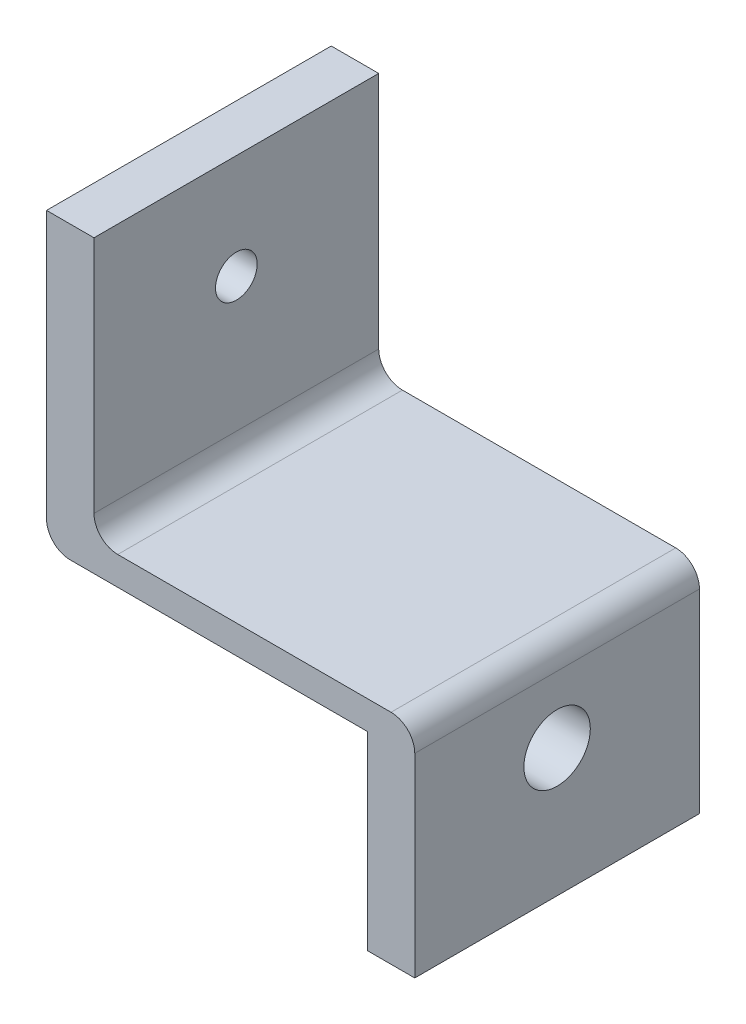
SolidWorks part; units mm, degrees
material "6061-T6 Al"
ref_plane "Front Plane" through (0, 0, 0) normal (0, 0, 1) x (1, 0, 0)
ref_plane "Top Plane" through (0, 0, 0) normal (0, 1, 0) x (1, 0, 0)
ref_plane "Right Plane" through (0, 0, 0) normal (1, 0, 0) x (0, 0, -1)
sketch "Sketch1" plane through (0, 0, 0) normal (0, 0, 1) x (1, 0, 0)
  line L0 (0, 0) -> (33.8, 0)
  line L1 (0, 0) -> (0, 30.65)
  line L2 (33.8, 0) -> (33.8, -20)
  dimension "D1" = 30.65
  dimension "D2" = 33.8
  dimension "D3" = 20
extrude "Extrude-Thin1" add sketch "Sketch1" against normal blind 30 thin thin type one direction wall 5
hole_wizard "Ø7.0 (7) Diameter Hole1" positions "3DSketch1" profile "Sketch2" hole size "Ø7.0" standard "Ansi Metric" end condition through all
sketch3d "3DSketch1"
  line L2 (38.8, -20, -30) -> (38.8, 5, -30) construction
  point P0 (38.8, -6.5, -15)
  dimension "D1" = 15
  dimension "D2" = 6.5
sketch "Sketch2" plane through (38.8, -6.5, -15) normal (0, 1, 0) x (0, 0, -1)
  line L0 (0, 0) -> (0, 38.8)
  line L1 (0, 38.8) -> (3.5, 38.8)
  line L2 (3.5, 38.8) -> (3.5, 0)
  line L5 (3.5, 0) -> (0, 0)
  line L11 (0, -6.35) -> (0, 107.95) construction
  dimension "Thru Hole Dia." = 7
  dimension "Thru Hole Depth" = 38.8
hole_wizard "Tapped Hole for #8-32 Helicoil1" positions "3DSketch2" profile "Sketch3" tap size "#8-32" standard "Helicoil® Inch" end condition through all
sketch3d "3DSketch2"
  line L0 (5, 5, -30) -> (5, 30.65, -30) construction
  line L1 (5, 30.65, -30) -> (5, 30.65, 0) construction
  point P0 (5, 19.65, -15)
  dimension "D1" = 15
  dimension "D2" = 11
sketch "Sketch3" plane through (5, 19.65, -15) normal (0, 1, 0) x (0, 0, -1)
  line L0 (0, 0) -> (0, 5)
  line L1 (0, 5) -> (2.1971, 5)
  line L2 (2.1971, 5) -> (2.1971, 0)
  line L5 (2.1971, 0) -> (0, 0)
  line L11 (0, -6.35) -> (0, 107.95) construction
  dimension "Thru Tap Drill Dia." = 4.3942
  dimension "Thru Tap Drill Depth" = 5
cosmetic thread "Hole Thread1" parameters "D1"=5, "D2"=5.2756
sketch "Sketch5" plane through (0, 0, 0) normal (0, 0, 1) x (1, 0, 0)
  line L0 (38.8, 5) -> (5, 5) construction
  line L1 (5, 35.2389) -> (48.8, 35.2389)
  line L2 (5, 35.2389) -> (5, 3)
  line L3 (5, 3) -> (48.8, 3)
  line L4 (48.8, 35.2389) -> (48.8, 3)
  line L5 (5, 5) -> (5, 30.65) construction
  line L6 (38.8, -20) -> (38.8, 5) construction
  dimension "D1" = 2
  dimension "D2" = 0
  dimension "D3" = 10
extrude "Extrude1" cut sketch "Sketch5" against normal through all
fillet "Fillet1" radius 2.5 3 edges at (0, 0, -15) (38.8, 3, -15) (5, 3, -15)
